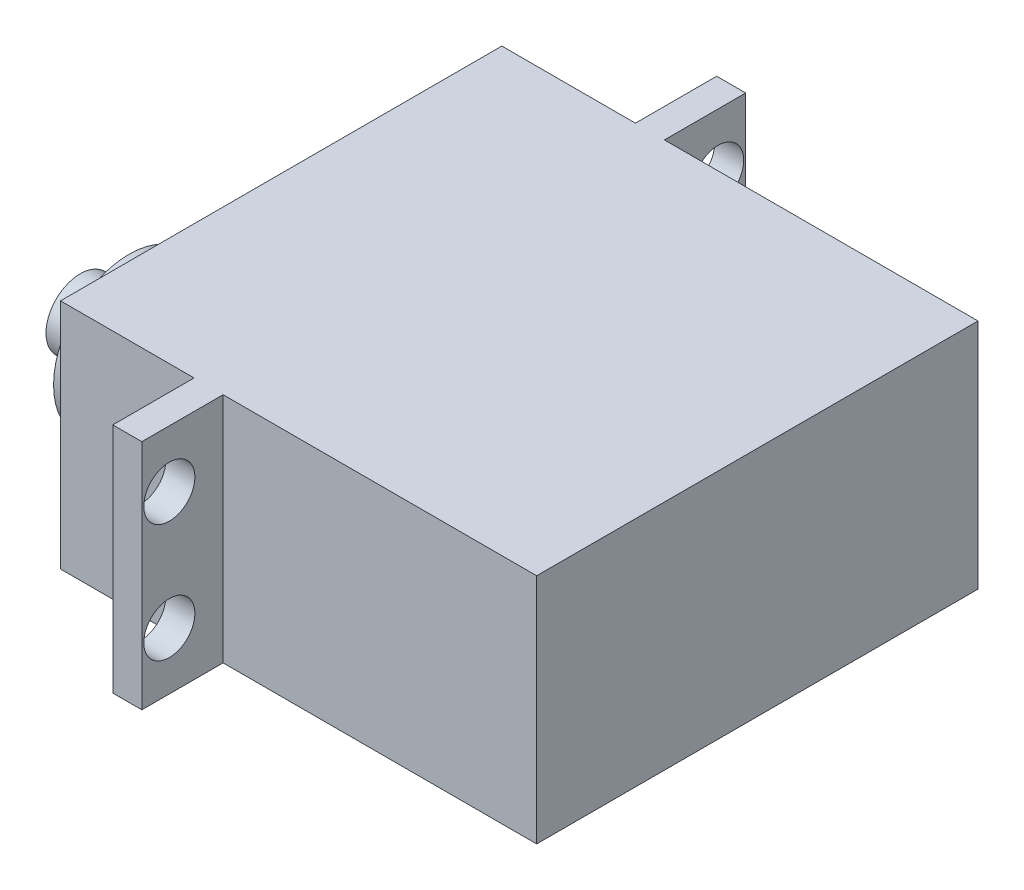
SolidWorks part; units mm, degrees
ref_plane "Front Plane" through (0, 0, 0) normal (0, 0, 1) x (1, 0, 0)
ref_plane "Top Plane" through (0, 0, 0) normal (0, 1, 0) x (1, 0, 0)
ref_plane "Right Plane" through (0, 0, 0) normal (1, 0, 0) x (0, 0, -1)
sketch "Sketch1" plane through (0, 0, 0) normal (0, 0, 1) x (1, 0, 0)
  line L1 (-20.0202, 9.7756) -> (20.9798, 9.7756)
  line L2 (-20.0202, 9.7756) -> (-20.0202, -10.2244)
  line L3 (-20.0202, -10.2244) -> (20.9798, -10.2244)
  line L4 (20.9798, 9.7756) -> (20.9798, -10.2244)
  dimension "D1" = 20
  dimension "D2" = 41
extrude "Extrude1" add sketch "Sketch1" along normal blind 38
sketch "Sketch2" plane through (0, 9.7756, 0) normal (0, 1, 0) x (1, 0, 0)
  line L0 (20.9798, -38) -> (20.9798, 0) construction
  line L1 (-8.5202, 7) -> (-6.0202, 7)
  line L2 (-8.5202, 7) -> (-8.5202, -45)
  line L3 (-8.5202, -45) -> (-6.0202, -45)
  line L4 (-6.0202, 7) -> (-6.0202, -45)
  line L5 (20.9798, 0) -> (-20.0202, 0) construction
  line L6 (20.9798, -38) -> (-20.0202, -38) construction
  dimension "D1" = 2.5
  dimension "D2" = 27
  dimension "D3" = 7
  dimension "D4" = 7
extrude "Extrude2" add sketch "Sketch2" against normal up to surface (20 mm away) up to face at (0.4798, -10.2244, 19)
sketch "Sketch3" plane through (-20.0202, 0, 0) normal (-1, 0, 0) x (0, 0, 1)
  line L0 (38, 9.7756) -> (38, -10.2244) construction
  circle A0 centre (28.3, 0) radius 6.5
  dimension "D1" = 13
  dimension "D2" = 9.7
extrude "Extrude3" add sketch "Sketch3" along normal blind 3.8
sketch "Sketch4" plane through (-23.8202, 0, 0) normal (-1, 0, 0) x (0, 0, 1)
  circle A0 centre (28.3, 0) radius 2.95
  circle A1 centre (28.3, 0) radius 6.5 construction
  dimension "D1" = 5.9
extrude "Extrude4" add sketch "Sketch4" along normal blind 4.2
hole_wizard "Ø4.4 (4.4) Diameter Hole1" positions "3DSketch1" profile "Sketch7" hole size "Ø4.4" standard "Ansi Metric"
sketch3d "3DSketch1"
  line L6 (-8.5202, -0.2244, -7) -> (-8.5202, -0.2244, 0) construction
  line L7 (-8.5202, -10.2244, -7) -> (-8.5202, 9.7756, -7) construction
  line L8 (-8.5202, 9.7756, 0) -> (-8.5202, -10.2244, 0) construction
  line L10 (-8.5202, 4.8606, -4.63) -> (-8.5202, -5.3094, -4.63) construction
  line L12 (-8.5202, -5.3094, -4.63) -> (-8.5202, -5.3094, -7) construction
  line L14 (-8.5202, -5.3094, 42.63) -> (-8.5202, -5.3094, 45) construction
  line L15 (-8.5202, -10.2244, 45) -> (-8.5202, 9.7756, 45) construction
  point P0 (-8.5202, 4.8606, -4.63)
  point P2 (-8.5202, -5.3094, -4.63)
  point P28 (-8.5202, -0.2244, -4.63)
  point P31 (-8.5202, 4.8606, 42.63)
  point P33 (-8.5202, -5.3094, 42.63)
  dimension "D1" = 10.17
  dimension "D2" = 47.26
sketch "Sketch7" plane through (-8.5202, 4.8606, -4.63) normal (0, 1, 0) x (0, 0, 1)
  line L0 (0, 0) -> (0, 151.3219)
  line L1 (0, 151.3219) -> (2.2, 150)
  line L2 (2.2, 150) -> (2.2, 0)
  line L5 (2.2, 0) -> (0, 0)
  line L10 (0, 151.3219) -> (-2.2, 150) construction
  line L11 (0, -6.35) -> (0, 107.95) construction
  dimension "Hole Dia." = 4.4
  dimension "Hole Depth" = 150
  dimension "Drill Angle" = 118
